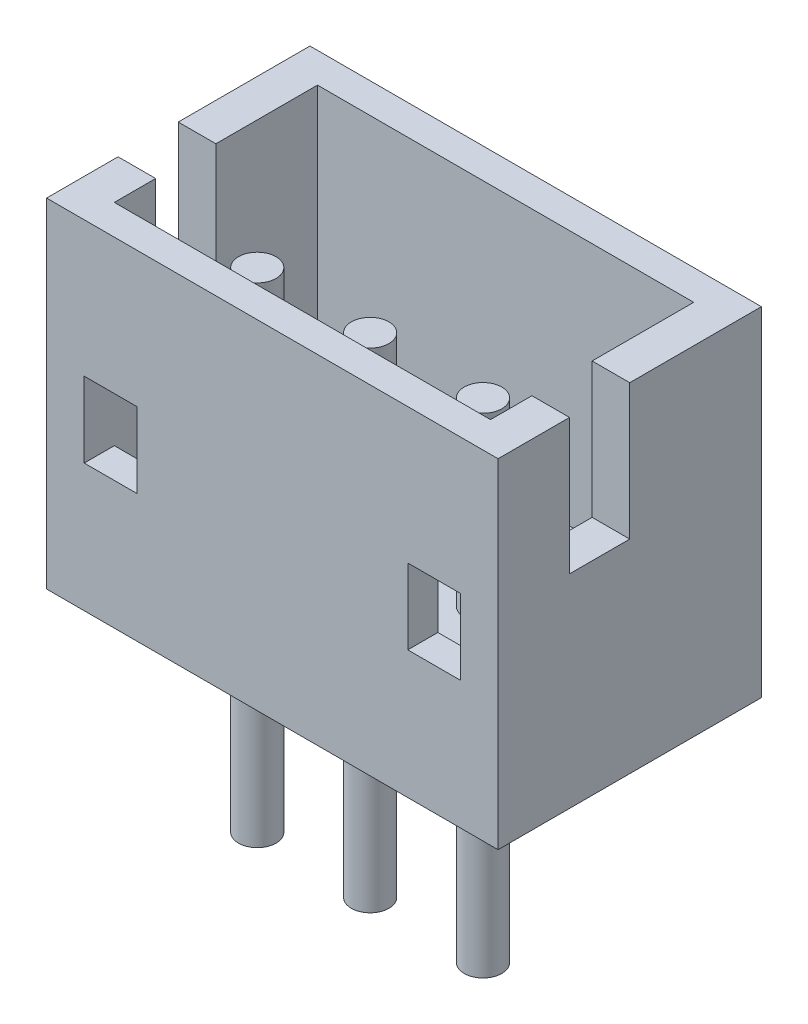
SolidWorks part; units mm, degrees
ref_plane "Front Plane" through (0, 0, 0) normal (0, 0, 1) x (1, 0, 0)
ref_plane "Top Plane" through (0, 0, 0) normal (0, 1, 0) x (1, 0, 0)
ref_plane "Right Plane" through (0, 0, 0) normal (1, 0, 0) x (0, 0, -1)
sketch "Sketch1" plane through (0, 0, 0) normal (0, 0, 1) x (1, 0, 0)
  line L0 (1.8, 4.5) -> (-1.8, 4.5)
  line L1 (-1.8, 4.5) -> (-1.8, 1.7)
  line L2 (-1.8, 1.7) -> (1.8, 1.7)
  line L3 (1.8, 1.7) -> (1.8, 4.5)
extrude "Boss-Extrude1" add sketch "Sketch1" against normal blind 0.4
sketch "Sketch2" plane through (-1.8, 0, 0) normal (-1, 0, 0) x (0, 0, 1)
  line L0 (-0.4, 2.7) -> (-0.4, 4.5)
  line L1 (-0.4, 4.5) -> (0, 4.5)
  line L2 (0, 4.5) -> (0, 2.7)
  line L3 (0, 2.7) -> (-0.4, 2.7)
extrude "Boss-Extrude2" add sketch "Sketch2" along normal blind 0.7
sketch "Sketch3" plane through (1.8, 0, 0) normal (1, 0, 0) x (0, 0, -1)
  line L0 (0, 4.5) -> (0.4, 4.5)
  line L1 (0.4, 4.5) -> (0.4, 2.7)
  line L2 (0.4, 2.7) -> (0, 2.7)
  line L3 (0, 2.7) -> (0, 4.5)
extrude "Boss-Extrude3" add sketch "Sketch3" along normal blind 0.7
sketch "Sketch4" plane through (2.5, 0, 0) normal (1, 0, 0) x (0, 0, -1)
  line L0 (0, 1.7) -> (0, 4.5)
  line L1 (0, 4.5) -> (3.1, 4.5)
  line L2 (3.1, 4.5) -> (3.1, 1.7)
  line L3 (3.1, 1.7) -> (0, 1.7)
extrude "Boss-Extrude4" add sketch "Sketch4" along normal blind 0.5
sketch "Sketch5" plane through (0, 1.7, 0) normal (0, -1, 0) x (1, 0, 0)
  line L0 (-2.5, -3.1) -> (-2.5, 0)
  line L1 (-2.5, 0) -> (3, 0)
  line L2 (3, 0) -> (3, -3.1)
  line L3 (3, -3.1) -> (-2.5, -3.1)
extrude "Boss-Extrude5" add sketch "Sketch5" along normal blind 1.7
sketch "Sketch6" plane through (-2.5, 0, 0) normal (-1, 0, 0) x (0, 0, 1)
  line L0 (-3.1, 0) -> (-3.1, 4.5)
  line L1 (-3.1, 4.5) -> (0, 4.5)
  line L2 (0, 4.5) -> (0, 0)
  line L3 (0, 0) -> (-3.1, 0)
extrude "Boss-Extrude6" add sketch "Sketch6" along normal blind 0.5
sketch "Sketch7" plane through (0, 0, -3.1) normal (0, 0, -1) x (-1, 0, 0)
  line L0 (-3, 4.5) -> (3, 4.5)
  line L1 (3, 4.5) -> (3, 0)
  line L2 (3, 0) -> (-3, 0)
  line L3 (-3, 0) -> (-3, 4.5)
extrude "Boss-Extrude7" add sketch "Sketch7" along normal blind 0.4
sketch "Sketch8" plane through (0, 1.7, 0) normal (0, 1, 0) x (-1, 0, 0)
  line L0 (-2.5, -0.4) -> (-2.5, -3.1)
  line L1 (-2.5, -3.1) -> (2.5, -3.1)
  line L2 (2.5, -3.1) -> (2.5, -0.4)
  line L3 (2.5, -0.4) -> (-2.5, -0.4)
extrude "Cut-Extrude1" cut sketch "Sketch8" against normal blind 0.6
sketch "Sketch9" plane through (2.5, 0, 0) normal (-1, 0, 0) x (0, 0, 1)
  line L0 (-0.4, 1.4) -> (-0.4, 1.1)
  line L1 (-0.4, 1.1) -> (-2.05, 1.1)
  line L2 (-2.05, 1.1) -> (-1.75, 1.4)
  line L3 (-1.75, 1.4) -> (-0.4, 1.4)
extrude "Boss-Extrude8" add sketch "Sketch9" along normal blind 5
sketch "Sketch10" plane through (3, 0, 0) normal (1, 0, 0) x (0, 0, -1)
  line L0 (1.75, 4.5) -> (0.95, 4.5)
  line L1 (0.95, 4.5) -> (0.95, 2.7)
  line L2 (0.95, 2.7) -> (1.75, 2.7)
  line L3 (1.75, 2.7) -> (1.75, 4.5)
extrude "Cut-Extrude2" cut sketch "Sketch10" against normal up to next
sketch "Sketch11" plane through (-3, 0, 0) normal (-1, 0, 0) x (0, 0, 1)
  line L0 (-0.95, 4.5) -> (-1.75, 4.5)
  line L1 (-1.75, 4.5) -> (-1.75, 2.7)
  line L2 (-1.75, 2.7) -> (-0.95, 2.7)
  line L3 (-0.95, 2.7) -> (-0.95, 4.5)
extrude "Cut-Extrude3" cut sketch "Sketch11" against normal through all
ref_plane "Plane1" through (0, 0, -1.3) normal (0, 0, -1) x (-1, 0, 0)
sketch "Sketch12" plane through (0, 0, -1.3) normal (0, 0, -1) x (-1, 0, 0)
  line L0 (1.25, -2.7) -> (1.5, -2.7)
  line L1 (1.5, -2.7) -> (1.5, 0)
  line L2 (1.5, 0) -> (1.25, 0)
  line L3 (1.25, 0) -> (1.25, -2.7)
  line L4 (1.5, -2.7) -> (1.5, 0) construction
revolve "Revolve1" add sketch "Sketch12" angle 360 about L4
sketch "Sketch13" plane through (0, 0, -1.3) normal (0, 0, -1) x (-1, 0, 0)
  line L0 (-0.25, -2.7) -> (0, -2.7)
  line L1 (0, -2.7) -> (0, 0)
  line L2 (0, 0) -> (-0.25, 0)
  line L3 (-0.25, 0) -> (-0.25, -2.7)
  line L4 (0, -2.7) -> (0, 0) construction
revolve "Revolve2" add sketch "Sketch13" angle 360 about L4
sketch "Sketch14" plane through (0, 0, -1.3) normal (0, 0, -1) x (-1, 0, 0)
  line L0 (-1.75, -2.7) -> (-1.5, -2.7)
  line L1 (-1.5, -2.7) -> (-1.5, 0)
  line L2 (-1.5, 0) -> (-1.75, 0)
  line L3 (-1.75, 0) -> (-1.75, -2.7)
  line L4 (-1.5, -2.7) -> (-1.5, 0) construction
revolve "Revolve3" add sketch "Sketch14" angle 360 about L4
sketch "Sketch15" plane through (0, 0, -1.3) normal (0, 0, -1) x (-1, 0, 0)
  line L0 (-1.75, 1.4) -> (-1.5, 1.4)
  line L1 (-1.5, 1.4) -> (-1.5, 3.8)
  line L2 (-1.5, 3.8) -> (-1.75, 3.8)
  line L3 (-1.75, 3.8) -> (-1.75, 1.4)
  line L4 (-1.5, 1.4) -> (-1.5, 3.8) construction
revolve "Revolve4" add sketch "Sketch15" angle 360 about L4
sketch "Sketch16" plane through (0, 0, -1.3) normal (0, 0, -1) x (-1, 0, 0)
  line L0 (-0.25, 1.4) -> (0, 1.4)
  line L1 (0, 1.4) -> (0, 3.8)
  line L2 (0, 3.8) -> (-0.25, 3.8)
  line L3 (-0.25, 3.8) -> (-0.25, 1.4)
  line L4 (0, 1.4) -> (0, 3.8) construction
revolve "Revolve5" add sketch "Sketch16" angle 360 about L4
sketch "Sketch17" plane through (0, 0, -1.3) normal (0, 0, -1) x (-1, 0, 0)
  line L0 (1.25, 1.4) -> (1.5, 1.4)
  line L1 (1.5, 1.4) -> (1.5, 3.8)
  line L2 (1.5, 3.8) -> (1.25, 3.8)
  line L3 (1.25, 3.8) -> (1.25, 1.4)
  line L4 (1.5, 1.4) -> (1.5, 3.8) construction
revolve "Revolve6" add sketch "Sketch17" angle 360 about L4
